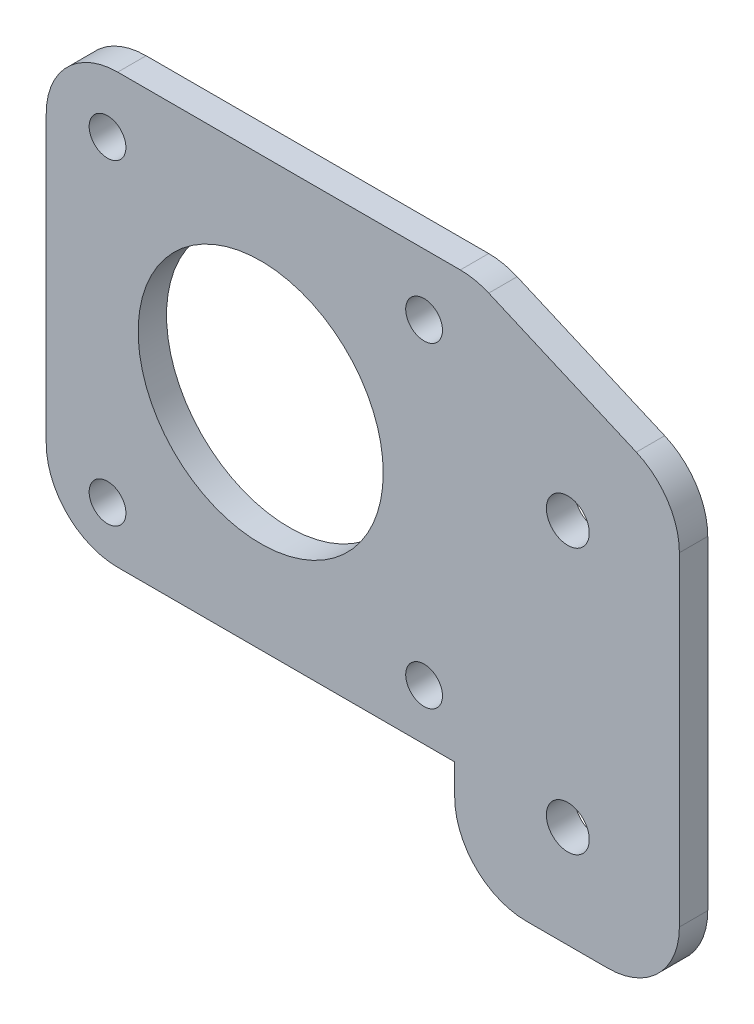
SolidWorks part; units mm, degrees
ref_plane "Front Plane" through (0, 0, 0) normal (0, 0, 1) x (1, 0, 0)
ref_plane "Top Plane" through (0, 0, 0) normal (0, 1, 0) x (1, 0, 0)
ref_plane "Right Plane" through (0, 0, 0) normal (1, 0, 0) x (0, 0, -1)
sketch "Sketch1" plane through (0, 0, 0) normal (0, 0, 1) x (1, 0, 0)
  line L1 (-62, 30.4655) -> (0, 30.4655)
  line L2 (-62, 30.4655) -> (-62, -21.5345)
  line L3 (-62, -21.5345) -> (0, -21.5345)
  line L4 (0, 30.4655) -> (0, -21.5345)
  dimension "D1" = 62
  dimension "D2" = 52
extrude "Boss-Extrude1" add sketch "Sketch1" along normal blind 2.7781
sketch "Sketch2" plane through (0, 0, 2.7781) normal (0, 0, 1) x (1, 0, 0)
  line L1 (-62, -21.5345) -> (-22, -21.5345)
  line L2 (-62, -21.5345) -> (-62, -11.5345)
  line L3 (-62, -11.5345) -> (-22, -11.5345)
  line L4 (-22, -21.5345) -> (-22, -11.5345)
  dimension "D1" = 40
  dimension "D2" = 10
sketch "Sketch3" plane through (0, 0, 2.7781) normal (0, 0, 1) x (1, 0, 0)
  line L0 (-20, 30.4655) -> (0, 21.8025)
  line L7 (-20, 30.4655) -> (0, 30.4655)
  line L8 (0, 30.4655) -> (0, 21.8025)
extrude "Cut-Extrude1" cut sketch "Sketch3" against normal blind 10
extrude "Cut-Extrude2" cut sketch "Sketch2" against normal blind 10
fillet "Fillet1" radius 7 4 edges at (0, -21.5345, 1.3891) (-22, -21.5345, 1.3891) (-62, -11.5345, 1.3891) (-62, 30.4655, 1.3891)
fillet "Fillet2" radius 7 2 edges at (-20, 30.4655, 1.3891) (0, 21.8025, 1.3891)
sketch "Sketch4" plane through (0, 0, 2.7781) normal (0, 0, 1) x (1, 0, 0)
  line L0 (-15, -21.5345) -> (-7, -21.5345) construction
  line L1 (-62, 23.4655) -> (-62, -4.5345) construction
  line L2 (-21.4509, 30.4655) -> (-55, 30.4655) construction
  line L3 (0, -14.5345) -> (0, 17.2061) construction
  circle A0 centre (-10.926, -11.5345) radius 2.1
  circle A1 centre (-10.926, 14.4655) radius 2.1
  circle A2 centre (-56, -6.5345) radius 1.8
  circle A3 centre (-56, 24.4655) radius 1.8
  circle A4 centre (-25, 24.4655) radius 1.8
  circle A5 centre (-25, -6.5345) radius 1.8
  circle A6 centre (-41, 9.4682) radius 12
  dimension "D1" = 26
  dimension "D3" = 31
  dimension "D5" = 6
  dimension "D10" = 21
  dimension "D11" = 3.6
  dimension "D12" = 3.6
  dimension "D13" = 3.6
  dimension "D14" = 3.6
  dimension "D16" = 4.2
  dimension "D17" = 4.2
  dimension "D18" = 24
  dimension "D2" = 10
  dimension "D4" = 31
  dimension "D6" = 6
  dimension "D7" = 31
  dimension "D8" = 6
  dimension "D9" = 6
  dimension "D15" = 10.926
  dimension "D19" = 20.9973
extrude "Cut-Extrude3" cut sketch "Sketch4" against normal blind 10
